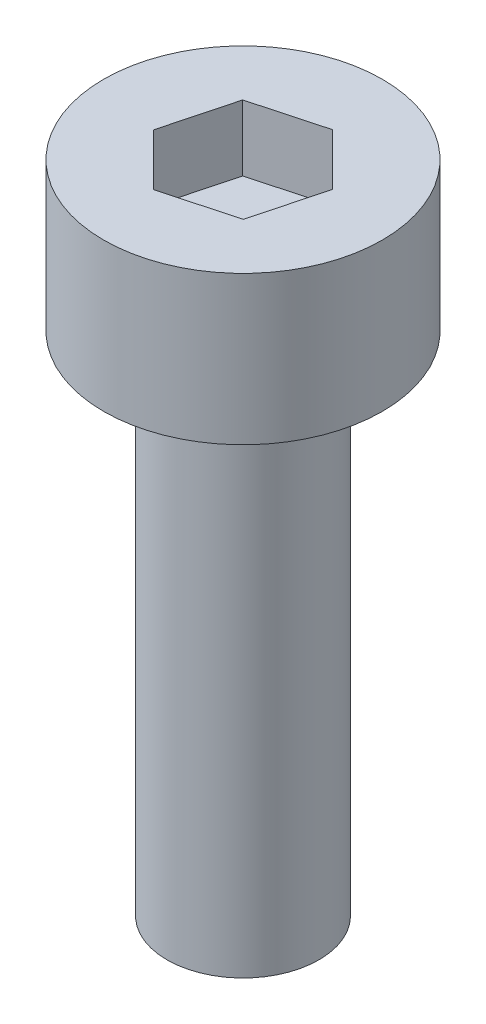
SolidWorks part; units mm, degrees
ref_plane "前视基准面" through (0, 0, 0) normal (0, 0, 1) x (1, 0, 0)
ref_plane "上视基准面" through (0, 0, 0) normal (0, 1, 0) x (1, 0, 0)
ref_plane "右视基准面" through (0, 0, 0) normal (1, 0, 0) x (0, 0, -1)
sketch "草图1" plane through (0, 0, 0) normal (0, 1, 0) x (1, 0, 0)
  circle A0 centre (0, 0) radius 1.5
  dimension "D1" = 3
extrude "凸台-拉伸1" add sketch "草图1" along normal blind 10
sketch "草图2" plane through (0, 10, 0) normal (0, 1, 0) x (1, 0, 0)
  circle A0 centre (0, 0) radius 2.75
  dimension "D1" = 5.5
extrude "凸台-拉伸2" add sketch "草图2" along normal blind 2.93
sketch "草图3" plane through (0, 12.93, 0) normal (0, 1, 0) x (1, 0, 0)
  line L1 (1.024, -1.0172) -> (1.3929, 0.3782)
  line L2 (1.3929, 0.3782) -> (0.3689, 1.3954)
  line L3 (0.3689, 1.3954) -> (-1.024, 1.0172)
  line L4 (-1.024, 1.0172) -> (-1.3929, -0.3782)
  line L5 (-1.3929, -0.3782) -> (-0.3689, -1.3954)
  line L6 (-0.3689, -1.3954) -> (1.024, -1.0172)
  circle A0 centre (0, 0) radius 1.25 construction
  dimension "D1" = 2.5
extrude "切除-拉伸1" cut sketch "草图3" against normal blind 1.3
